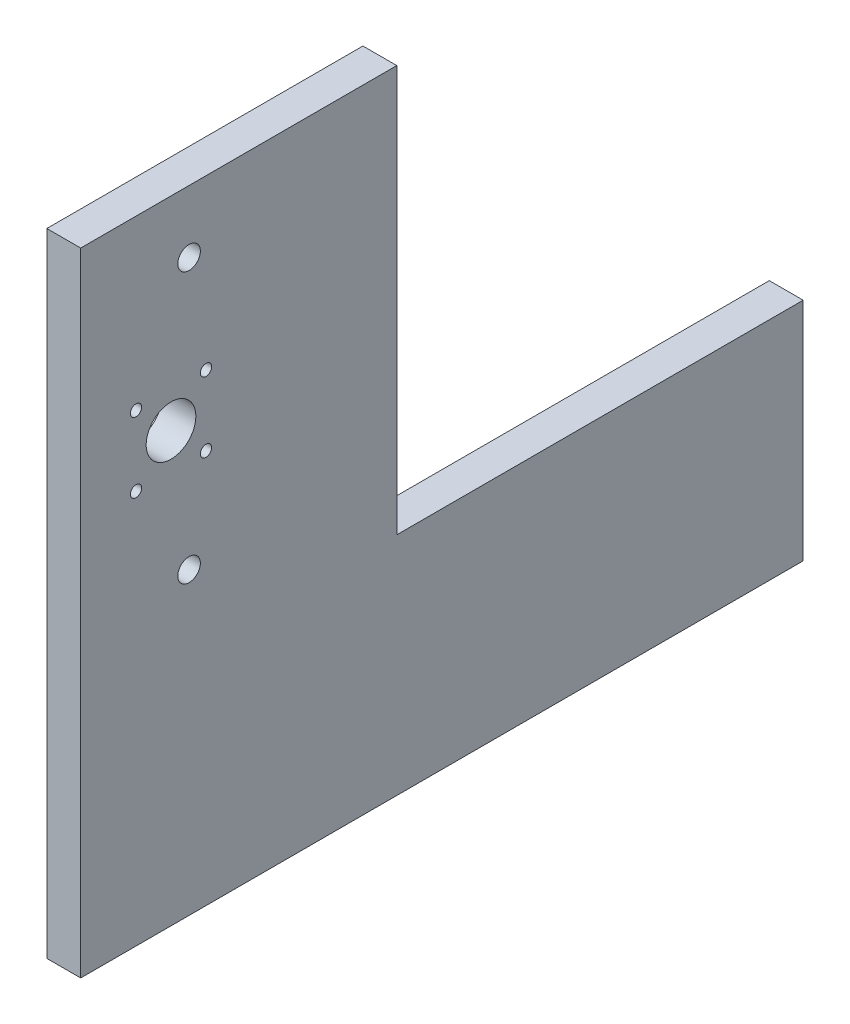
SolidWorks part; units mm, degrees
material "Balsa"
ref_plane "Front Plane" through (0, 0, 0) normal (0, 0, 1) x (1, 0, 0)
ref_plane "Top Plane" through (0, 0, 0) normal (0, 1, 0) x (1, 0, 0)
ref_plane "Right Plane" through (0, 0, 0) normal (1, 0, 0) x (0, 0, -1)
sketch "side sketch" plane through (0, 0, 0) normal (1, 0, 0) x (0, 0, -1)
  line L0 (15.1288, -90.6072) -> (15.1288, 189.3928)
  line L1 (15.1288, 189.3928) -> (155.1288, 189.3928)
  line L2 (155.1288, 189.3928) -> (155.1288, 9.3928)
  line L3 (155.1288, 9.3928) -> (335.1288, 9.3928)
  line L4 (335.1288, 9.3928) -> (335.1288, -90.6072)
  line L5 (335.1288, -90.6072) -> (15.1288, -90.6072)
  circle A0 centre (55.1288, 99.3928) radius 11
  circle A1 centre (39.6288, 114.8928) radius 2.5
  circle A2 centre (70.6288, 114.8928) radius 2.5
  circle A3 centre (70.6288, 83.8928) radius 2.5
  circle A4 centre (39.6288, 83.8928) radius 2.5
  circle A5 centre (63.1288, 161.7693) radius 5
  circle A6 centre (63.1288, 42.042) radius 5
  point P19 (55.1288, 99.3928)
  dimension "D5" = 22
  dimension "D6" = 15.5
  dimension "D8" = 5
  dimension "D1" = 280
  dimension "D2" = 100
  dimension "D3" = 320
  dimension "D4" = 140
  dimension "D7" = 15.5
  dimension "D10" = 190
  dimension "D11" = 40
  dimension "D9" = 4
extrude "Boss-Extrude1" add sketch "side sketch" along normal blind 15
